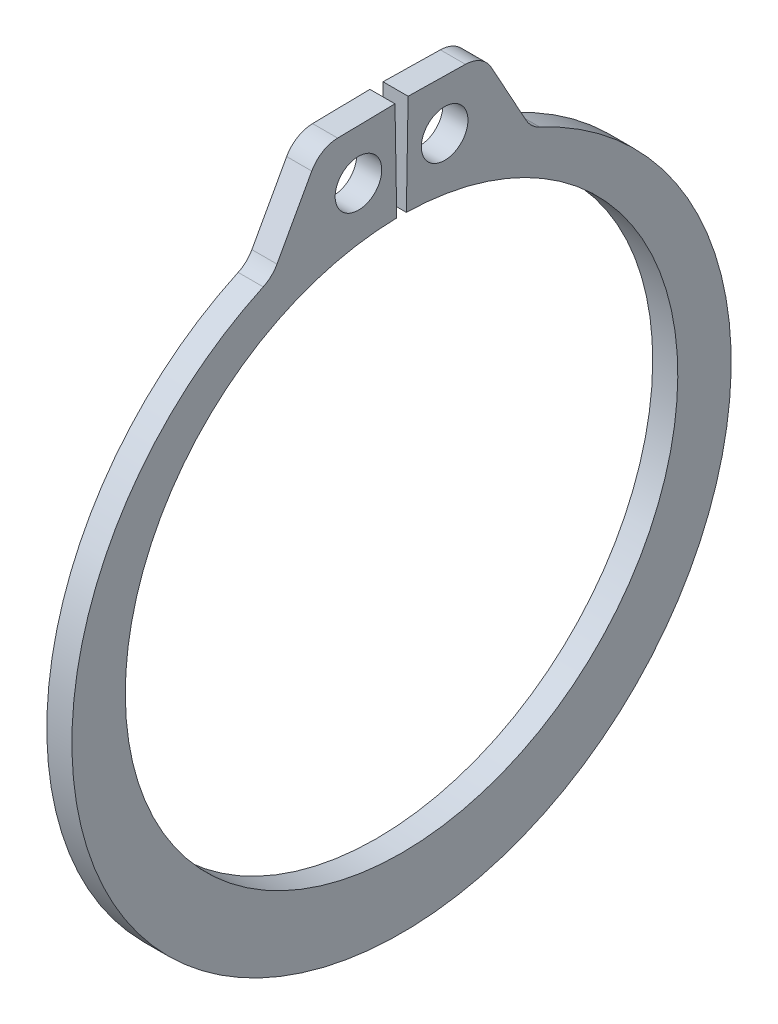
SolidWorks part; units mm, degrees
material "Cast Carbon Steel"
ref_plane "Front" through (0, 0, 0) normal (0, 0, 1) x (1, 0, 0)
ref_plane "Top" through (0, 0, 0) normal (0, 1, 0) x (1, 0, 0)
ref_plane "Right" through (0, 0, 0) normal (1, 0, 0) x (0, 0, -1)
sketch "Sketch1" plane through (0, 0, 0) normal (1, 0, 0) x (0, 0, -1)
  line L0 (0, 0) -> (0, 11.7475) construction
  line L1 (-0.205, 11.7457) -> (-0.2791, 15.9869)
  line L2 (0.2791, 15.9869) -> (3.4599, 15.9313)
  line L3 (3.4599, 15.9313) -> (5.5053, 12.2152)
  line L4 (0.205, 11.7457) -> (0.2791, 15.9869)
  line L5 (-0.2791, 15.9869) -> (-3.4599, 15.9313)
  line L6 (-3.4599, 15.9313) -> (-5.5053, 12.2152)
  line L7 (-5.5053, 12.2152) -> (-4.8269, 10.71) construction
  line L8 (5.5053, 12.2152) -> (4.8269, 10.71) construction
  line L9 (0, -11.7475) -> (0, -14.6939) construction
  line L10 (-3.4599, 15.9313) -> (-0.205, 11.7457) construction
  line L11 (0, 11.7475) -> (0, 15.9893) construction
  line L12 (-11.7475, 0) -> (11.7475, 0) construction
  circle A0 centre (0, 0) radius 11.7475 construction
  arc A1 (-0.205, 11.7457) -> (0.205, 11.7457) centre (0, 0) ccw
  circle A3 centre (0, 0) radius 17.526 construction
  circle A4 centre (-1.8325, 13.8385) radius 0.9906
  circle A5 centre (1.8325, 13.8385) radius 0.9906
  arc A6 (-5.5053, 12.2152) -> (5.5053, 12.2152) centre (0, -0.6762) ccw
  point P0 (0, -14.6939)
  dimension "A" = 23.495
  dimension "D2" = 3.1813
  dimension "L" = 35.052
  dimension "Hole" = 1.9812
  dimension "Smin" = 1.651
  dimension "Smax" = 2.9464
  dimension "H" = 4.2418
  dimension "Angle" = 1
extrude "Extrude1" add sketch "Sketch1" along normal mid plane 1.0668
fillet "Fillet1" radius 1.2827 4 edges at (0, 12.2152, 5.5053) (0, 12.2152, -5.5053) (0, 15.9313, 3.4599) (0, 15.9313, -3.4599)
sketch "Sketch2" plane through (0, 0, 0) normal (0, 0, 1) x (1, 0, 0)
  line L0 (-5.9182, 0) -> (15.4178, 0)
  line L1 (15.4178, 0) -> (15.4178, -12.7)
  line L2 (-0.5842, -12.7) -> (-5.1562, -12.7)
  line L3 (15.4178, -12.7) -> (0.5842, -12.7)
  line L4 (0.5842, -12.7) -> (0.5842, -11.938)
  line L5 (0.5842, -11.938) -> (-0.5842, -11.938)
  line L6 (-0.5842, -11.938) -> (-0.5842, -12.7)
  line L7 (-0.5842, -12.7) -> (-5.9182, -12.7) construction
  line L8 (-5.9182, -12.7) -> (-5.9182, 0) construction
  line L9 (15.4178, 0) -> (76.391, 0) construction
  line L10 (-5.1562, -12.7) -> (-5.9182, -11.938)
  line L11 (-5.9182, -11.938) -> (-5.9182, 0)
  point P10 (0, -11.938)
  dimension "D1" = 45
  dimension "Dg" = 23.876
  dimension "Ds" = 25.4
  dimension "W" = 1.1684
  dimension "D2" = 21.336
  dimension "D3" = 5.334
revolve "Revolve1" [suppressed] add sketch "Sketch2" angle 360 about L9
delete or keep bodies "Body-Delete1" [suppressed] type delete bodies bodies 122
equation "\"D2@Sketch2\" = \"D1@Extrude1\"*20"
equation "\"D3@Sketch2\" = \"D2@Sketch2\"/4"
equation "\"D2@Sketch1\" = \"H@Sketch1\"*.75"
